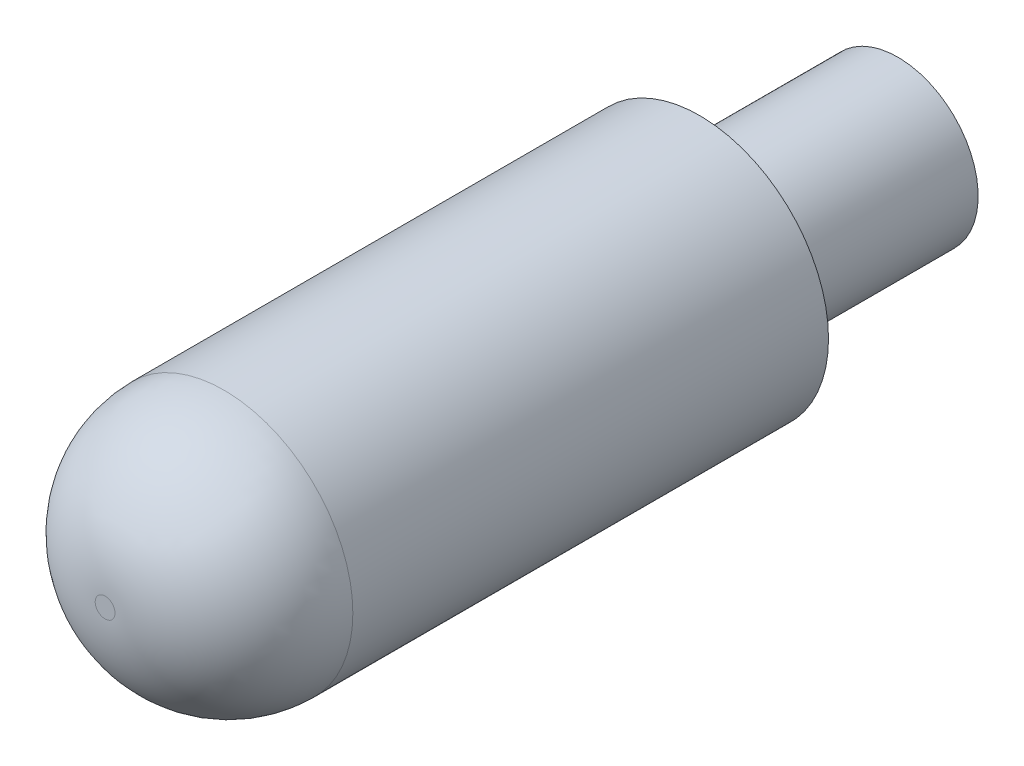
SolidWorks part; units mm, degrees
ref_plane "Plan de face" through (0, 0, 0) normal (0, 0, 1) x (1, 0, 0)
ref_plane "Plan de dessus" through (0, 0, 0) normal (0, 1, 0) x (1, 0, 0)
ref_plane "Plan de droite" through (0, 0, 0) normal (1, 0, 0) x (0, 0, -1)
sketch "Esquisse1" plane through (0, 0, 0) normal (0, 0, 1) x (1, 0, 0)
  circle A0 centre (0, 0) radius 6.5
  dimension "D1" = 13
extrude "Boss.-Extru.1" add sketch "Esquisse1" along normal blind 30
sketch "Esquisse2" plane through (0, 0, 0) normal (0, 0, -1) x (-1, 0, 0)
  circle A0 centre (0, 0) radius 4.05
  dimension "D1" = 8.1
extrude "Boss.-Extru.2" add sketch "Esquisse2" along normal blind 10
fillet "Congé4" radius 6 1 edges at (6.5, 0, 30)
